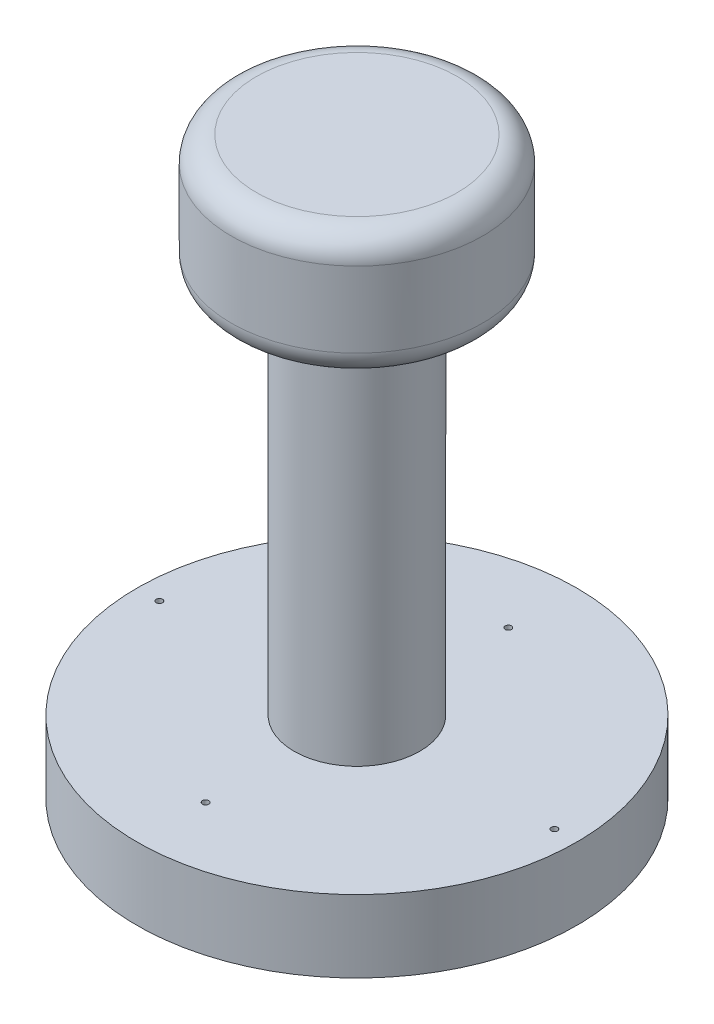
SolidWorks part; units mm, degrees
ref_plane "Front Plane" through (0, 0, 0) normal (0, 0, 1) x (1, 0, 0)
ref_plane "Top Plane" through (0, 0, 0) normal (0, 1, 0) x (1, 0, 0)
ref_plane "Right Plane" through (0, 0, 0) normal (1, 0, 0) x (0, 0, -1)
sketch "Sketch1" plane through (0, 0, 0) normal (0, 0, 1) x (1, 0, 0)
  line L1 (-5, -5) -> (5, -5)
  line L2 (-5, -5) -> (-5, 5)
  line L3 (-5, 5) -> (5, 5)
  line L4 (5, -5) -> (5, 5)
  line L5 (-5, -5) -> (5, 5) construction
  line L6 (-5, 5) -> (5, -5) construction
  point P0 (0, 0)
  dimension "D1" = 10
  dimension "D2" = 10
revolve "Revolve1" add sketch "Sketch1" angle 360 about L4
fillet "Fillet1" radius 2 1 edges at (5, 5, -10)
fillet "Fillet2" radius 2 1 edges at (5, -5, -10)
sketch "Sketch2" plane through (0, -5, 0) normal (0, -1, 0) x (-1, 0, 0)
  line L0 (2.8411, -1.5867) -> (-12.8411, 1.5867) construction
  circle A0 centre (-5, 0) radius 8 construction
  circle A1 centre (-5, 0) radius 5
extrude "Boss-Extrude1" add sketch "Sketch2" along normal blind 30
sketch "Sketch3" plane through (0, -35, 0) normal (0, -1, 0) x (-1, 0, 0)
  line L0 (0, 0) -> (-10, 0) construction
  circle A0 centre (-5, 0) radius 5 construction
  circle A1 centre (-5, 0) radius 17.5
extrude "Boss-Extrude2" add sketch "Sketch3" along normal blind 5
sketch "Sketch4" plane through (0, -40, 0) normal (0, -1, 0) x (-1, 0, 0)
  line L0 (12.5, 0) -> (-22.5, 0) construction
  circle A0 centre (-5, 0) radius 17.5 construction
  circle A1 centre (-5, 0) radius 17.5
  circle A2 centre (-5, 0) radius 17.25
extrude "Boss-Extrude4" add sketch "Sketch4" along normal blind 0.75
sketch "Sketch5" plane through (0, -40, 0) normal (0, -1, 0) x (-1, 0, 0)
  line L0 (12.25, 0) -> (-22.25, 0) construction
  line L2 (9.1785, 6.8356) -> (-19.1785, 6.8356)
  line L3 (9.1785, 6.8356) -> (9.1785, -6.8356)
  line L4 (9.1785, -6.8356) -> (-19.1785, -6.8356)
  line L5 (-19.1785, 6.8356) -> (-19.1785, -6.8356)
  line L6 (9.1785, 6.8356) -> (-19.1785, -6.8356) construction
  line L7 (9.1785, -6.8356) -> (-19.1785, 6.8356) construction
  line L8 (8.68, 6.3353) -> (-18.68, 6.3353)
  line L9 (8.68, 6.3353) -> (8.68, -6.3353)
  line L10 (8.68, -6.3353) -> (-18.68, -6.3353)
  line L11 (-18.68, 6.3353) -> (-18.68, -6.3353)
  line L12 (8.68, 6.3353) -> (-18.68, -6.3353) construction
  line L13 (8.68, -6.3353) -> (-18.68, 6.3353) construction
  circle A1 centre (-5, 0) radius 17.25 construction
  point P5 (-5, 0)
  point P10 (-5, 0)
  dimension "D1" = 28.3571
  dimension "D2" = 27.36
  dimension "D3" = 12.6706
  dimension "D4" = 13.6713
extrude "Boss-Extrude5" add sketch "Sketch5" along normal blind 0.75
fillet "Fillet3" radius 2 1 edges at (-8.68, -40.375, 6.3353)
fillet "Fillet4" radius 2 1 edges at (-9.1785, -40.375, 6.8356)
fillet "Fillet5" radius 2 1 edges at (18.68, -40.375, 6.3353)
fillet "Fillet6" radius 2 1 edges at (19.1785, -40.375, 6.8356)
fillet "Fillet9" radius 2 1 edges at (18.68, -40.375, -6.3353)
fillet "Fillet10" radius 2 1 edges at (19.1785, -40.375, -6.8356)
fillet "Fillet11" radius 2 1 edges at (-8.68, -40.375, -6.3353)
fillet "Fillet12" radius 2 1 edges at (-9.1785, -40.375, -6.8356)
sketch "Sketch8" plane through (0, -40, 0) normal (0, -1, 0) x (1, 0, 0)
  line L5 (-3.9483, -2.7234) -> (7.1306, -2.7234)
  line L6 (-3.9483, -2.7234) -> (-3.9483, -3.2234)
  line L7 (-3.9483, -3.2234) -> (7.1306, -3.2234)
  line L8 (7.1306, -2.7234) -> (7.1306, -3.2234)
  line L9 (-3.9483, -2.7234) -> (-3.4483, -2.7234)
  line L10 (-3.9483, -2.7234) -> (-3.9483, 0)
  line L11 (-3.9483, 0) -> (-3.4483, 0)
  line L12 (-3.4483, -2.7234) -> (-3.4483, 0)
  dimension "D1" = 0.5
  dimension "D2" = 0.5
extrude "Boss-Extrude7" add sketch "Sketch8" along normal blind 0.75 contours L5 L12 L11 L10
sketch "Sketch9" plane through (0, -40, 0) normal (0, -1, 0) x (-1, 0, 0)
  circle A0 centre (-17.461, -5.1331) radius 2.5165
  circle A1 centre (-14.9445, -8.6422) radius 1.5099
  circle A2 centre (-17.9699, -8.9369) radius 1.0109
extrude "Boss-Extrude8" add sketch "Sketch9" along normal blind 0.75
fillet "Fillet13" radius 2 1 edges at (-3.4483, -40.375, -2.7234)
fillet "Fillet14" radius 2 1 edges at (-3.9483, -40.375, -3.2234)
sketch "Sketch15" plane through (0, -40, 0) normal (0, -1, 0) x (-1, 0, 0)
  text T0 "N"
extrude "Boss-Extrude10" add sketch "Sketch15" along normal blind 0.75
sketch "Sketch16" plane through (0, -40, 0) normal (0, -1, 0) x (-1, 0, 0)
  text T0 "O"
extrude "Boss-Extrude11" add sketch "Sketch16" along normal blind 0.75
sketch "Sketch17" plane through (0, -40, 0) normal (0, -1, 0) x (-1, 0, 0)
  text T0 "C"
extrude "Boss-Extrude12" add sketch "Sketch17" along normal blind 0.75
sketch "Sketch19" plane through (0, -40, 0) normal (0, -1, 0) x (-1, 0, 0)
  text T0 "<r180>E</r>"
extrude "Boss-Extrude14" add sketch "Sketch19" along normal blind 0.75
sketch "Sketch20" plane through (0, -40, 0) normal (0, -1, 0) x (-1, 0, 0)
  line L0 (-5, -17.25) -> (-5, -6.8356) construction
  line L1 (-15.6079, -6.8356) -> (7.1785, -6.8356) construction
  line L2 (-5, 6.8356) -> (-5, 17.25) construction
  line L3 (7.1785, 6.8356) -> (-17.1785, 6.8356) construction
  line L4 (9.1785, 0) -> (10.7204, 0) construction
  line L5 (9.1785, -4.8356) -> (9.1785, 4.8356) construction
  line L6 (-20.7204, 0) -> (-19.1785, 0) construction
  line L7 (-19.1785, 4.8356) -> (-19.1785, -3.2939) construction
  circle A0 centre (-5, 0) radius 17.25 construction
  circle A1 centre (-5, 0) radius 17.25 construction
  circle A2 centre (-5, -12.0428) radius 0.25
  circle A3 centre (-5, 12.0428) radius 0.25
  circle A4 centre (-20.7204, 0) radius 0.25
  circle A5 centre (10.7204, 0) radius 0.25
  dimension "D1" = 1.5418
  dimension "D2" = 1.5418
extrude "Cut-Extrude1" cut sketch "Sketch20" against normal blind 5 contours A3
sketch "Sketch23" plane through (0, -40, 0) normal (0, -1, 0) x (-1, 0, 0)
  line L0 (-5, 11.7928) -> (-5, -17.25) construction
  line L1 (-5, -17.25) -> (-5, -6.8356) construction
  line L2 (-15.6079, -6.8356) -> (7.1785, -6.8356) construction
  circle A0 centre (-5, 12.0428) radius 0.25 construction
  circle A1 centre (-5, -12.0428) radius 0.25
extrude "Cut-Extrude2" cut sketch "Sketch23" against normal blind 5
sketch "Sketch24" plane through (0, -40, 0) normal (0, -1, 0) x (-1, 0, 0)
  line L0 (-19.1785, 0) -> (-22.25, 0) construction
  line L1 (-19.1785, 4.8356) -> (-19.1785, -3.2939) construction
  line L2 (9.1785, 0) -> (12.25, 0) construction
  line L3 (9.1785, -4.8356) -> (9.1785, 4.8356) construction
  circle A0 centre (-5, 0) radius 17.25 construction
  circle A1 centre (-5, 0) radius 17.25 construction
  circle A2 centre (10.7143, 0) radius 0.25
extrude "Cut-Extrude3" cut sketch "Sketch24" against normal blind 5
sketch "Sketch25" plane through (0, -40, 0) normal (0, -1, 0) x (-1, 0, 0)
  line L0 (-19.1785, 0) -> (-22.25, 0) construction
  line L1 (-19.1785, 4.8356) -> (-19.1785, -3.2939) construction
  circle A0 centre (-5, 0) radius 17.25 construction
  circle A1 centre (-20.7143, 0) radius 0.25
extrude "Cut-Extrude4" cut sketch "Sketch25" against normal blind 5
